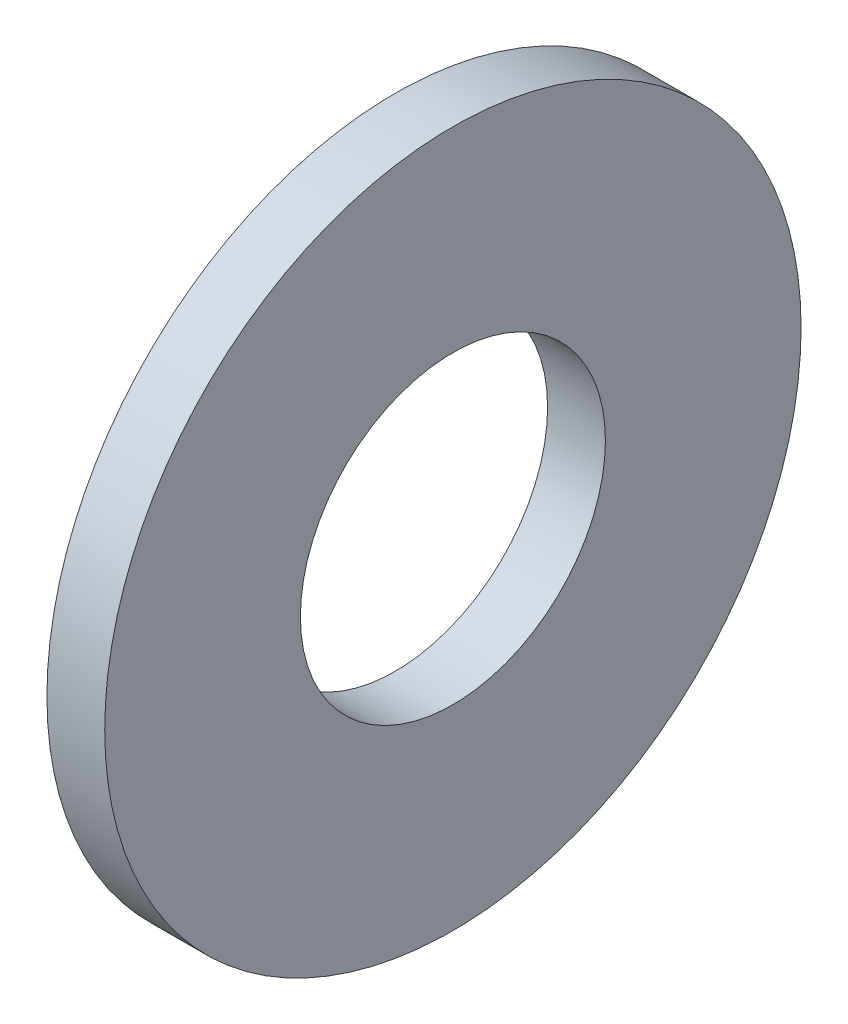
SolidWorks part; units mm, degrees
ref_plane "Front Plane" through (0, 0, 0) normal (0, 0, 1) x (1, 0, 0)
ref_plane "Top Plane" through (0, 0, 0) normal (0, 1, 0) x (1, 0, 0)
ref_plane "Right Plane" through (0, 0, 0) normal (1, 0, 0) x (0, 0, -1)
sketch "Sketch1" plane through (0, 0, 0) normal (0, 0, 1) x (1, 0, 0)
  line L0 (-34.925, 0) -> (9.525, 0) construction
  line L1 (0, 5.5626) -> (0, 12.7)
  line L2 (0, 12.7) -> (-2.1082, 12.7)
  line L3 (-2.1082, 12.7) -> (-2.1082, 5.5626)
  line L4 (-2.1082, 5.5626) -> (0, 5.5626)
  dimension "Thickness" = 2.1082
  dimension "Inside_dia" = 11.1252
  dimension "Outside_dia" = 25.4
revolve "Revolve1" add sketch "Sketch1" angle 360 about L0
